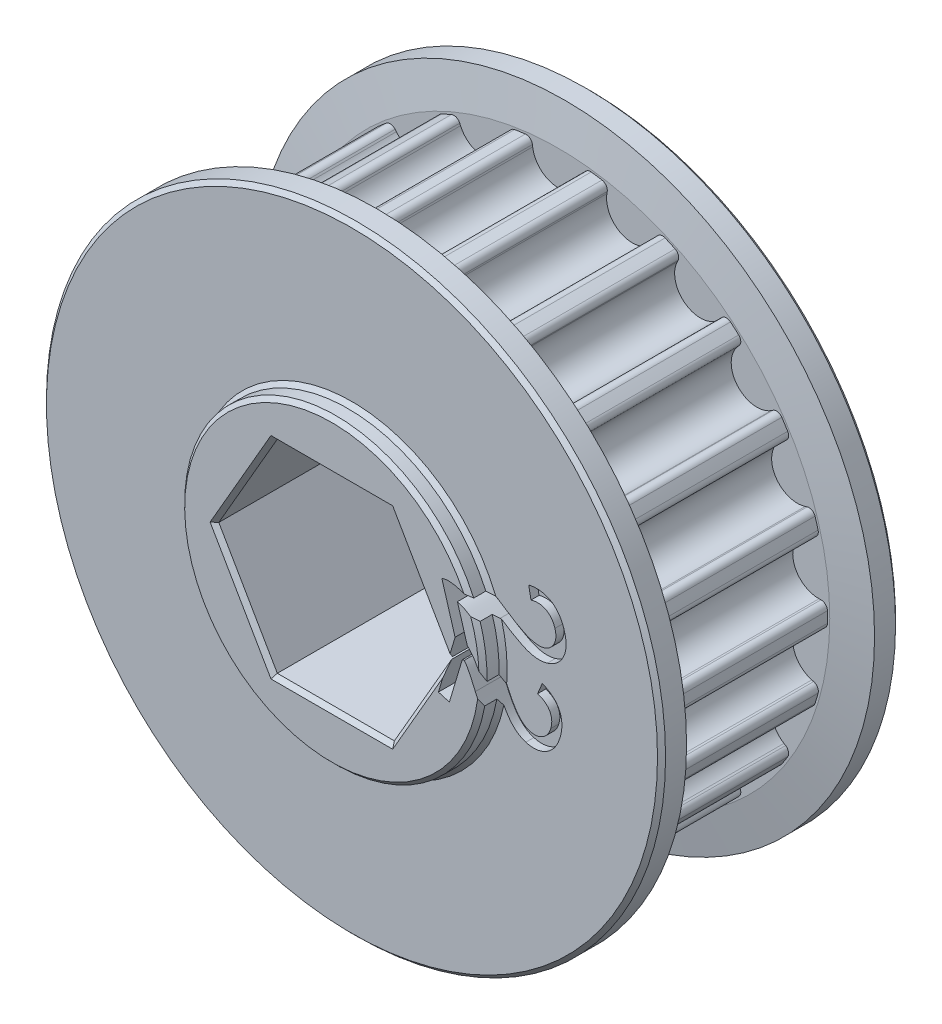
SolidWorks part; units mm, degrees
material "ABS"
ref_plane "Front Plane" through (0, 0, 0) normal (0, 0, 1) x (1, 0, 0)
ref_plane "Top Plane" through (0, 0, 0) normal (0, 1, 0) x (1, 0, 0)
ref_plane "Right Plane" through (0, 0, 0) normal (1, 0, 0) x (0, 0, -1)
sketch "Sketch2" plane through (0, 0, 0) normal (0, 0, 1) x (1, 0, 0)
  circle A0 centre (0, 0) radius 16.9667
  dimension "D1" = 33.9334
extrude "pulley" add sketch "Sketch2" along normal mid plane 11
sketch "tooth" plane through (0, 0, 0) normal (0, 0, 1) x (1, 0, 0)
  line L0 (0, 0) -> (0, 16.5667) construction
  line L1 (4.9427, 15.8122) -> (0, 16.5667) construction
  line L2 (4.9427, 15.8122) -> (0, 0) construction
  line L3 (-2.1327, 20.6023) -> (-1.6129, 16.3686)
  line L6 (2.1327, 20.6023) -> (1.6129, 16.3686)
  line L7 (-2.1327, 20.6023) -> (2.1327, 20.6023)
  arc A1 (-1.6129, 16.3686) -> (1.6129, 16.3686) centre (0, 16.5667) ccw
  arc A2 (0, 16.5667) -> (4.9427, 15.8122) centre (0, 0) cw construction
  circle A3 centre (4.9427, 15.8122) radius 1.625 construction
  dimension "D1" = 16.5667
  dimension "D2" = 3.25
  dimension "D3" = 5
  dimension "D5" = 14
extrude "cut tooth" cut sketch "tooth" against normal mid plane 11
fillet "blend tooth" radius 0.4 2 edges at (1.6761, 16.8837, 0) (-1.6761, 16.8837, 0)
pattern_circular "tooth pattern" count 22 over 360 about axis through (0, 0, 0) along (0, 0, 1) of "cut tooth", "blend tooth"
sketch "Sketch3" plane through (0, 0, 0) normal (0, 0, 1) x (1, 0, 0)
  circle A0 centre (0, 0) radius 19.5067
  circle A1 centre (0, 0) radius 16.9667 construction
  dimension "D1" = 2.54
extrude "sidewall" add sketch "Sketch3" along normal blind 2 from offset 5.5
mirror "mirror sidewall" about plane through (0, 0, 0) normal (0, 0, 1) of "sidewall"
chamfer "sidewall chamfer" distance 2.4 angle 10 2 edges at (19.5067, 0, 5.5) (19.5067, 0, -5.5)
sketch "Sketch5" plane through (0, 0, 0) normal (0, 0, 1) x (1, 0, 0)
  circle A0 centre (0, 0) radius 9.525
  dimension "D1" = 19.05
extrude "bearing spacer (Manual Suppress)" add sketch "Sketch5" along normal blind 8.77 and the other way blind 8.77
sketch "Sketch4" plane through (0, 0, 0) normal (0, 0, 1) x (1, 0, 0)
  line L1 (3.6882, 6.3881) -> (-3.6882, 6.3881)
  line L2 (-3.6882, 6.3881) -> (-7.3763, 0)
  line L3 (-7.3763, 0) -> (-3.6882, -6.3881)
  line L4 (-3.6882, -6.3881) -> (3.6882, -6.3881)
  line L5 (3.6882, -6.3881) -> (7.3763, 0)
  line L6 (7.3763, 0) -> (3.6882, 6.3881)
  circle A0 centre (0, 0) radius 6.3881 construction
  dimension "D1" = 12.7762
extrude "hex shaft" cut sketch "Sketch4" against normal mid plane 127
chamfer "chamfers" distance 0.254 angle 45 18 edges at (19.5067, 0, -7.5) (19.5067, 0, 7.5) (-9.525, 0, -7.5) (9.525, 0, 7.5) (9.525, 0, 8.77) (0, 6.3881, 8.77) (-5.5323, 3.194, 8.77) (-5.5323, -3.194, 8.77) (0, -6.3881, 8.77) (5.5323, -3.194, 8.77) (5.5323, 3.1941, 8.77) (9.525, 0, -8.77) (0, -6.3881, -8.77) (-5.5323, -3.194, -8.77) (-5.5323, 3.194, -8.77) (0, 6.3881, -8.77) (5.5323, 3.1941, -8.77) (5.5323, -3.194, -8.77)
sketch "SK-VersaCut" plane through (0, 0, 0) normal (0, 0, 1) x (1, 0, 0)
  line B0 (6.3387, 23.6565) -> (5.299, 19.7762)
  line B1 (14.4772, 14.4772) -> (17.3177, 17.3177)
  line B2 (23.6565, 6.3387) -> (19.7762, 5.299)
  line B3 (19.7762, -5.299) -> (23.6565, -6.3387)
  line B4 (17.3177, -17.3177) -> (14.4772, -14.4772)
  line B5 (5.299, -19.7762) -> (6.3387, -23.6565)
  line B6 (-6.3387, -23.6565) -> (-5.299, -19.7762)
  line B7 (-14.4772, -14.4772) -> (-17.3177, -17.3177)
  line B8 (-23.6565, -6.3387) -> (-19.7762, -5.299)
  line B9 (-19.7762, 5.299) -> (-23.6565, 6.3387)
  line B10 (-17.3177, 17.3177) -> (-14.4772, 14.4772)
  line B11 (-5.299, 19.7762) -> (-6.3387, 23.6565)
  circle B12 centre (0, 23.8125) radius 2.2479
  arc B13 (5.9535, 18.5765) -> (13.1109, 14.4442) centre (0, 0) cw
  arc B14 (7.5904, 24.3458) -> (17.2889, 18.7464) centre (0, 0) cw
  arc B15 (5.9535, 18.5765) -> (5.299, 19.7762) centre (6.2559, 19.5198) cw
  arc B16 (13.1109, 14.4442) -> (14.4772, 14.4772) centre (13.7767, 15.1777) ccw
  arc B17 (17.2889, 18.7464) -> (17.3177, 17.3177) centre (16.6173, 18.0182) cw
  arc B18 (7.5904, 24.3458) -> (6.3387, 23.6565) centre (7.2956, 23.4001) ccw
  circle B19 centre (20.6222, 11.9062) radius 2.2479
  arc B20 (19.0645, 4.1323) -> (19.0645, -4.1323) centre (0, 0) cw
  arc B21 (24.8793, 5.5994) -> (24.8793, -5.5994) centre (0, 0) cw
  arc B22 (19.0645, 4.1323) -> (19.7762, 5.299) centre (20.0326, 4.3422) cw
  arc B23 (19.0645, -4.1323) -> (19.7762, -5.299) centre (20.0326, -4.3422) ccw
  arc B24 (24.8793, -5.5994) -> (23.6565, -6.3387) centre (23.9129, -5.3819) cw
  arc B25 (24.8793, 5.5994) -> (23.6565, 6.3387) centre (23.9129, 5.3819) ccw
  circle B26 centre (20.6222, -11.9063) radius 2.2479
  arc B27 (13.1109, -14.4442) -> (5.9535, -18.5765) centre (0, 0) cw
  arc B28 (17.2889, -18.7464) -> (7.5904, -24.3458) centre (0, 0) cw
  arc B29 (13.1109, -14.4442) -> (14.4772, -14.4772) centre (13.7767, -15.1777) cw
  arc B30 (5.9535, -18.5765) -> (5.299, -19.7762) centre (6.2559, -19.5198) ccw
  arc B31 (7.5904, -24.3458) -> (6.3387, -23.6565) centre (7.2956, -23.4001) cw
  arc B32 (17.2889, -18.7464) -> (17.3177, -17.3177) centre (16.6173, -18.0182) ccw
  circle B33 centre (0, -23.8125) radius 2.2479
  arc B34 (-5.9535, -18.5765) -> (-13.1109, -14.4442) centre (0, 0) cw
  arc B35 (-7.5904, -24.3458) -> (-17.2889, -18.7464) centre (0, 0) cw
  arc B36 (-5.9535, -18.5765) -> (-5.299, -19.7762) centre (-6.2559, -19.5198) cw
  arc B37 (-13.1109, -14.4442) -> (-14.4772, -14.4772) centre (-13.7767, -15.1777) ccw
  arc B38 (-17.2889, -18.7464) -> (-17.3177, -17.3177) centre (-16.6173, -18.0182) cw
  arc B39 (-7.5904, -24.3458) -> (-6.3387, -23.6565) centre (-7.2956, -23.4001) ccw
  circle B40 centre (-20.6222, -11.9063) radius 2.2479
  arc B41 (-19.0645, -4.1323) -> (-19.0645, 4.1323) centre (0, 0) cw
  arc B42 (-24.8793, -5.5994) -> (-24.8793, 5.5994) centre (0, 0) cw
  arc B43 (-19.0645, -4.1323) -> (-19.7762, -5.299) centre (-20.0326, -4.3422) cw
  arc B44 (-19.0645, 4.1323) -> (-19.7762, 5.299) centre (-20.0326, 4.3422) ccw
  arc B45 (-24.8793, 5.5994) -> (-23.6565, 6.3387) centre (-23.9129, 5.3819) cw
  arc B46 (-24.8793, -5.5994) -> (-23.6565, -6.3387) centre (-23.9129, -5.3819) ccw
  circle B47 centre (-20.6222, 11.9063) radius 2.2479
  arc B48 (-13.1109, 14.4442) -> (-5.9535, 18.5765) centre (0, 0) cw
  arc B49 (-17.2889, 18.7464) -> (-7.5904, 24.3458) centre (0, 0) cw
  arc B50 (-13.1109, 14.4442) -> (-14.4772, 14.4772) centre (-13.7767, 15.1777) cw
  arc B51 (-5.9535, 18.5765) -> (-5.299, 19.7762) centre (-6.2559, 19.5198) ccw
  arc B52 (-7.5904, 24.3458) -> (-6.3387, 23.6565) centre (-7.2956, 23.4001) cw
  arc B53 (-17.2889, 18.7464) -> (-17.3177, 17.3177) centre (-16.6173, 18.0182) ccw
sketch_block_instance "VersaKey-1"
sketch_block "Block1" parameters "D1"=47.625, "D2"=4.4958, "D3"=19.5072, "D4"=25.5016, "D6"=0.9906, "D5"=30
extrude "VersaKey (Manual Suppress)" [suppressed] cut sketch "SK-VersaCut" against normal through all both and the other way through all
sketch "Lightening Holes" plane through (0, 0, 0) normal (0, 0, 1) x (1, 0, 0)
  line L0 (-3.0389, 10.3435) -> (-3.9521, 11.9253)
  line L1 (3.9521, 11.9253) -> (3.0389, 10.3435)
  line L14 (0, 0) -> (-3.6662, 6.35) construction
  line L15 (0, 0) -> (0, 6.35) construction
  line L24 (0, 0) -> (3.6662, 6.35) construction
  line L25 (0, 6.35) -> (-3.6662, 6.35) construction
  line L26 (0, 6.35) -> (3.6662, 6.35) construction
  line L27 (-3.0943, 11.43) -> (3.0943, 11.43)
  line L28 (0, 6.35) -> (0, 11.43) construction
  line L29 (7.4383, 7.8035) -> (8.3515, 9.3853)
  line L30 (8.3515, 8.3947) -> (11.4458, 3.0353)
  line L31 (12.3037, 2.54) -> (10.4772, 2.54)
  line L32 (10.4772, -2.54) -> (12.3037, -2.54)
  line L33 (11.4458, -3.0353) -> (8.3515, -8.3947)
  line L34 (8.3515, -9.3853) -> (7.4383, -7.8035)
  line L35 (3.0389, -10.3435) -> (3.9521, -11.9253)
  line L36 (3.0943, -11.43) -> (-3.0943, -11.43)
  line L37 (-3.9521, -11.9253) -> (-3.0389, -10.3435)
  line L38 (-7.4383, -7.8035) -> (-8.3515, -9.3853)
  line L39 (-8.3515, -8.3947) -> (-11.4458, -3.0353)
  line L40 (-12.3037, -2.54) -> (-10.4772, -2.54)
  line L41 (-10.4772, 2.54) -> (-12.3037, 2.54)
  line L42 (-11.4458, 3.0353) -> (-8.3515, 8.3947)
  line L43 (-8.3515, 9.3853) -> (-7.4383, 7.8035)
  arc A3 (-2.3764, 11.81) -> (2.3764, 11.81) centre (0, 0) cw
  arc A4 (-3.0943, 11.43) -> (-3.9521, 11.9253) centre (-3.0943, 12.4206) cw
  arc A5 (3.0943, 11.43) -> (3.9521, 11.9253) centre (3.0943, 12.4206) ccw
  arc A6 (2.3764, 11.81) -> (3.0389, 10.3435) centre (2.181, 10.8388) cw
  arc A7 (-2.3764, 11.81) -> (-3.0389, 10.3435) centre (-2.181, 10.8388) ccw
  arc A72 (9.0395, 7.963) -> (11.4159, 3.8469) centre (0, 0) cw
  arc A73 (9.0395, 7.963) -> (7.4383, 7.8035) centre (8.2962, 7.3082) ccw
  arc A74 (8.3515, 8.3947) -> (8.3515, 9.3853) centre (9.2094, 8.89) cw
  arc A75 (11.4159, 3.8469) -> (10.4772, 2.54) centre (10.4772, 3.5306) cw
  arc A76 (11.4159, -3.8469) -> (9.0395, -7.963) centre (0, 0) cw
  arc A77 (11.4159, -3.8469) -> (10.4772, -2.54) centre (10.4772, -3.5306) ccw
  arc A78 (11.4458, -3.0353) -> (12.3037, -2.54) centre (12.3037, -3.5306) cw
  arc A79 (9.0395, -7.963) -> (7.4383, -7.8035) centre (8.2962, -7.3082) cw
  arc A80 (2.3764, -11.81) -> (-2.3764, -11.81) centre (0, 0) cw
  arc A81 (2.3764, -11.81) -> (3.0389, -10.3435) centre (2.181, -10.8388) ccw
  arc A82 (3.0943, -11.43) -> (3.9521, -11.9253) centre (3.0943, -12.4206) cw
  arc A83 (-2.3764, -11.81) -> (-3.0389, -10.3435) centre (-2.181, -10.8388) cw
  arc A84 (-9.0395, -7.963) -> (-11.4159, -3.8469) centre (0, 0) cw
  arc A85 (-9.0395, -7.963) -> (-7.4383, -7.8035) centre (-8.2962, -7.3082) ccw
  arc A86 (-8.3515, -8.3947) -> (-8.3515, -9.3853) centre (-9.2094, -8.89) cw
  arc A87 (-11.4159, -3.8469) -> (-10.4772, -2.54) centre (-10.4772, -3.5306) cw
  arc A88 (-11.4159, 3.8469) -> (-9.0395, 7.963) centre (0, 0) cw
  arc A89 (-11.4159, 3.8469) -> (-10.4772, 2.54) centre (-10.4772, 3.5306) ccw
  arc A90 (-11.4458, 3.0353) -> (-12.3037, 2.54) centre (-12.3037, 3.5306) cw
  arc A91 (-9.0395, 7.963) -> (-7.4383, 7.8035) centre (-8.2962, 7.3082) cw
  arc A92 (11.4458, 3.0353) -> (12.3037, 2.54) centre (12.3037, 3.5306) ccw
  arc A93 (8.3515, -8.3947) -> (8.3515, -9.3853) centre (9.2094, -8.89) ccw
  arc A94 (-3.0943, -11.43) -> (-3.9521, -11.9253) centre (-3.0943, -12.4206) ccw
  arc A95 (-11.4458, -3.0353) -> (-12.3037, -2.54) centre (-12.3037, -3.5306) ccw
  arc A96 (-8.3515, 8.3947) -> (-8.3515, 9.3853) centre (-9.2094, 8.89) ccw
  point P72 (0, 0)
  point P77 (0, 0)
  point P87 (0, 0)
  dimension "D4" = 12.0467
  dimension "D6" = 0.9906
  dimension "D5" = 2.54
  dimension "D7" = 60
  dimension "D1" = 6.35
  dimension "D3" = 5.08
  dimension "D2" = 6
extrude "Lightening Holes (Man Suppress)" [suppressed] cut sketch "Lightening Holes" against normal through all both and the other way through all
sketch "Sketch6" plane through (0, 0, 0) normal (0, 0, 1) x (1, 0, 0)
  line L0 (0, 8.1927) -> (0, 0) construction
  line L1 (0, 0) -> (0, -8.1927) construction
  arc A1 (0, 8.1927) -> (0, -8.1927) centre (0, 0) cw construction
  arc A2 (0, 8.1927) -> (0, -8.1927) centre (0, 0) ccw construction
  text T0 "22" font "DS-Digital" height in points 24
extrude "4419" cut sketch "Sketch6" along normal blind 2.54 from offset 6.992
equation "\"INPUT_pulley_teeth\"= 22"
equation "\"pulley_c2c\"= 5mm"
equation "\"pulley_teeth_deg\"= 360 / \"INPUT_pulley_teeth\""
equation "\"pulley_radius\"= ( \"pulley_c2c\" / ( 2 * cos ( \"iso_half_angle\" ) ) ) - 1mm"
equation "\"iso_half_angle\"= ( 180 - \"pulley_teeth_deg\" ) / 2"
equation "\"D1@tooth\" = \"pulley_radius\""
equation "\"pulley_tooth_dia\"= 3.25mm"
equation "\"D3@tooth\"=\"pulley_c2c\""
equation "\"D2@tooth\"=\"pulley_tooth_dia\""
equation "\"D1@Sketch2\"=2* \"pulley_radius\"+\"pulley_tooth_offset\""
equation "\"pulley_tooth_offset\"= .8mm"
equation "\"D1@tooth pattern\" = \"INPUT_pulley_teeth\""
equation "\"INPUT_pulley_belt_9_or_15_(unitless)\"= 9"
equation "\"D1@pulley\"=\"pulley_width\""
equation "\"D19@sidewall\" =  ( \"pulley_width\" / 2 ) "
equation "\"D1@sidewall\"=\"pulley_sidewall_thick\""
equation "\"pulley_width\"= IIF ( \"INPUT_pulley_belt_9_or_15_(unitless)\" = 9 , 11mm , 17mm )"
equation "\"D1@cut tooth\"=\"pulley_width\""
equation "\"D1@sidewall chamfer\" = 2.4mm"
equation "\"D4@Lightening Holes\"=\"pulley_radius\"-\"pulley_tooth_dia\"-.05"
equation "\"D1@bearing spacer (Manual Suppress)\" = 0.05 +  ( \"pulley_width\" / 2 )  + \"pulley_sidewall_thick\""
equation "\"D2@bearing spacer (Manual Suppress)\" = 0.05 +  ( \"pulley_width\" / 2 )  + \"pulley_sidewall_thick\""
equation "\"pulley_sidewall_thick\"= 2mm"
equation "\"D1@4419\" = \"pulley_width\""
equation "\"D19@4419\"=(\"pulley_width\" / 2) +\"pulley_sidewall_thick\" - 0.02"
equation "\"rad_len\" = \"INPUT_pulley_teeth\" * \"pulley_c2c\""
